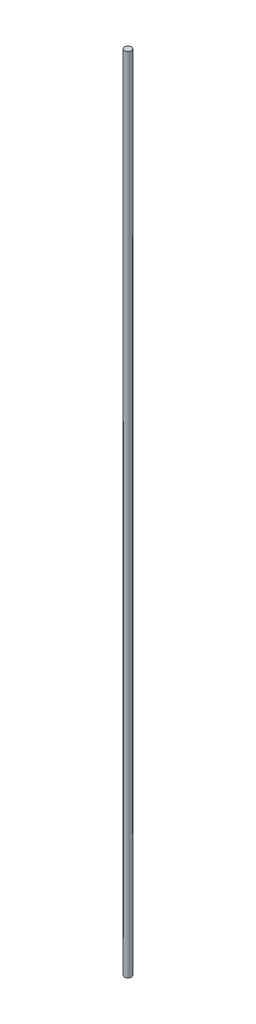
SolidWorks part; units mm, degrees
ref_plane "Płaszczyzna przednia" through (0, 0, 0) normal (0, 0, 1) x (1, 0, 0)
ref_plane "Płaszczyzna górna" through (0, 0, 0) normal (0, 1, 0) x (1, 0, 0)
ref_plane "Płaszczyzna prawa" through (0, 0, 0) normal (1, 0, 0) x (0, 0, -1)
sketch "Sketch1" plane through (0, 0, 0) normal (0, 1, 0) x (1, 0, 0)
  circle A0 centre (0, 0) radius 25.5
extrude "Boss-Extrude1" add sketch "Sketch1" along normal blind 6000
